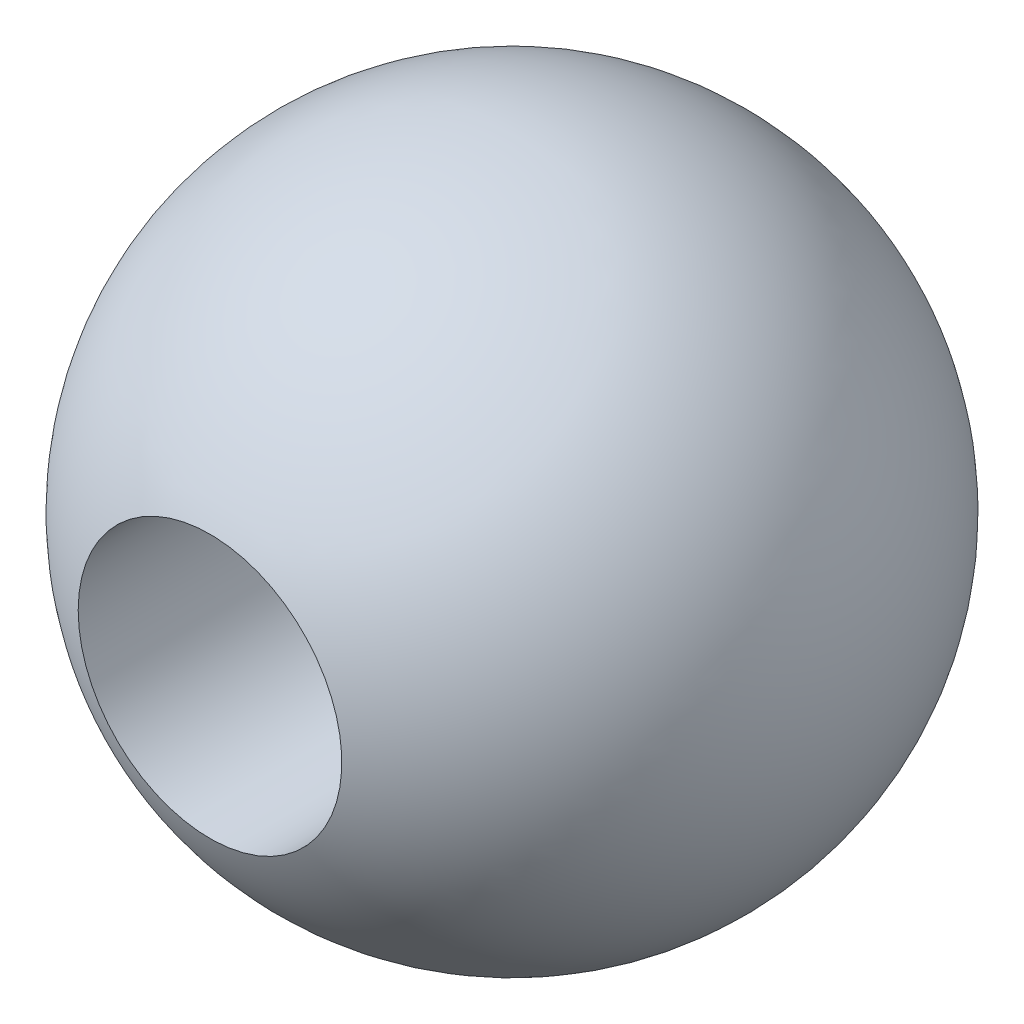
SolidWorks part; units mm, degrees
ref_plane "Front Plane" through (0, 0, 0) normal (0, 0, 1) x (1, 0, 0)
ref_plane "Top Plane" through (0, 0, 0) normal (0, 1, 0) x (1, 0, 0)
ref_plane "Right Plane" through (0, 0, 0) normal (1, 0, 0) x (0, 0, -1)
sketch "Sketch1" plane through (0, 0, 0) normal (0, 0, 1) x (1, 0, 0)
  line L0 (0, 6.35) -> (0, -6.35)
  arc A0 (0, -6.35) -> (0, 6.35) centre (0, 0) ccw
  dimension "D1" = 12.7
revolve "Revolve1" add sketch "Sketch1" angle 360 about L0
sketch "Sketch2" plane through (0, 0, 0) normal (0, 0, 1) x (1, 0, 0)
  circle A0 centre (0, 0) radius 2.54
  circle A1 centre (0, 0) radius 6.35 construction
  dimension "D1" = 5.08
extrude "Cut-Extrude1" cut sketch "Sketch2" against normal through all both and the other way through all
